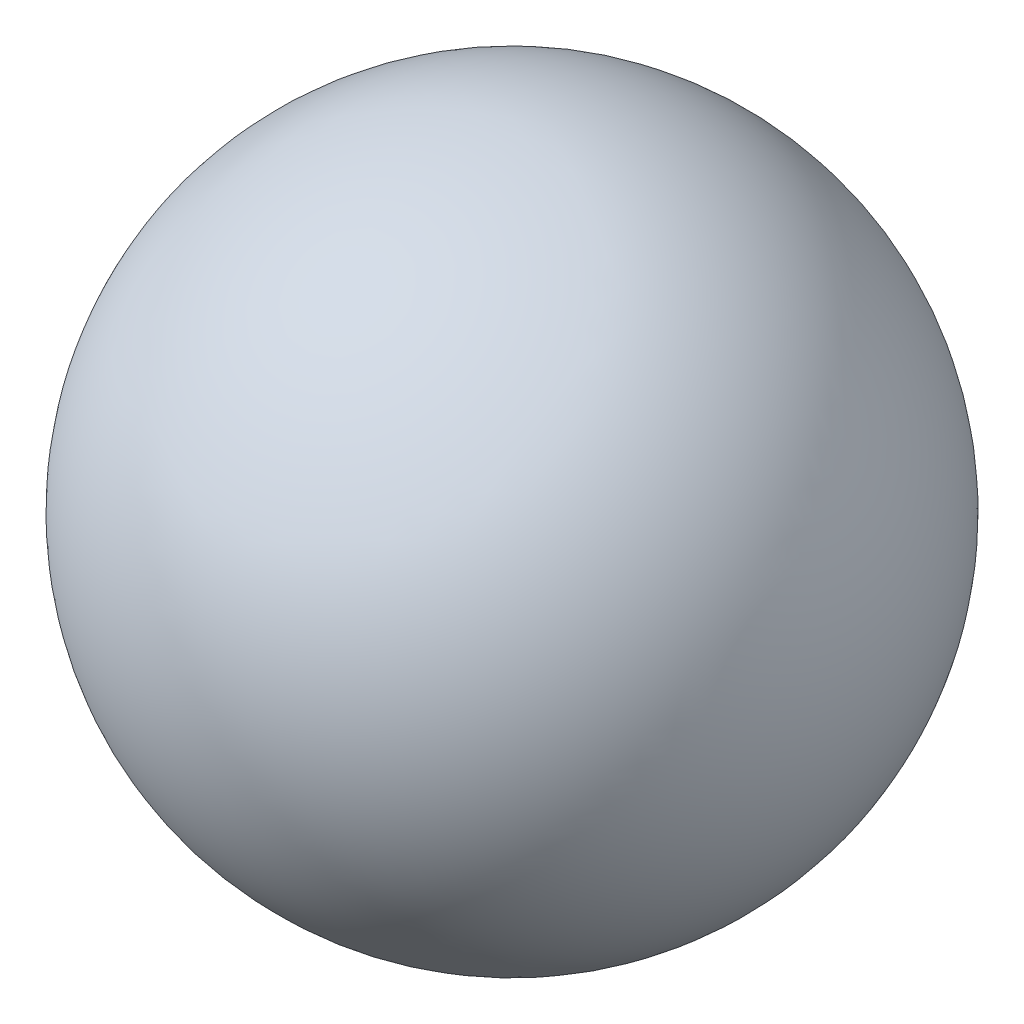
SolidWorks part; units mm, degrees
ref_plane "Front Plane" through (0, 0, 0) normal (0, 0, 1) x (1, 0, 0)
ref_plane "Top Plane" through (0, 0, 0) normal (0, 1, 0) x (1, 0, 0)
ref_plane "Right Plane" through (0, 0, 0) normal (1, 0, 0) x (0, 0, -1)
sketch "Sketch2" plane through (0, 0, 0) normal (0, 1, 0) x (1, 0, 0)
  line L0 (-1.5, 0) -> (1.5, 0)
  arc A1 (1.5, 0) -> (-1.5, 0) centre (0, 0) ccw
revolve "Revolve1" add sketch "Sketch2" angle 360 about L0
